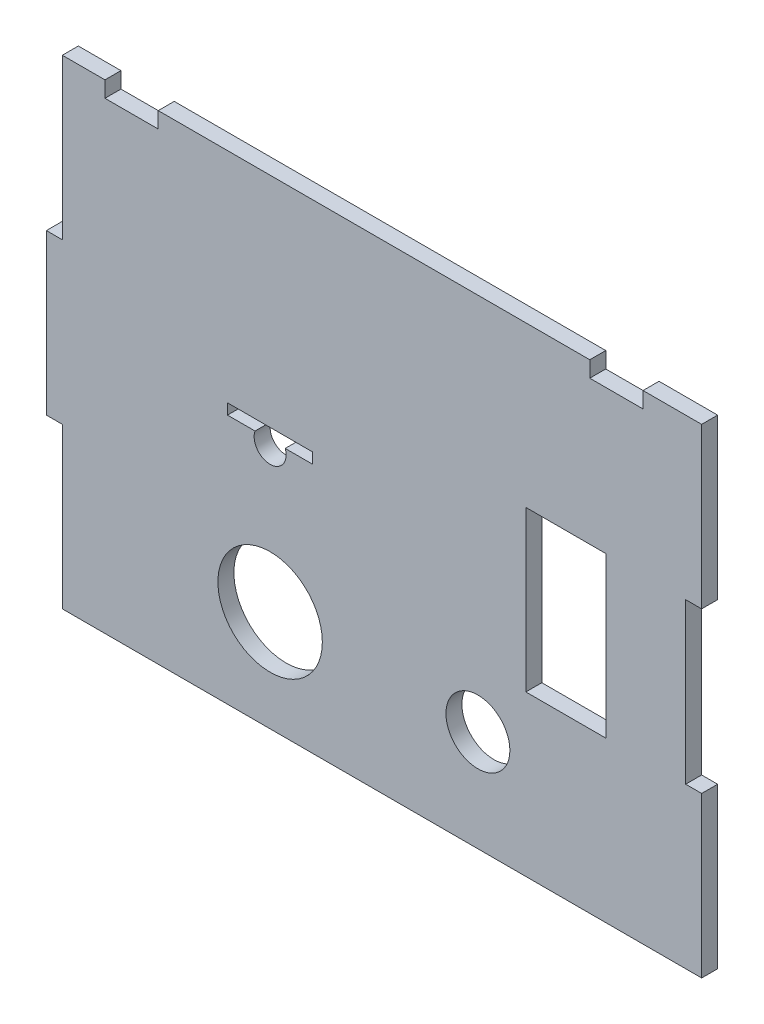
SolidWorks part; units mm, degrees
ref_plane "Front Plane" through (0, 0, 0) normal (0, 0, 1) x (1, 0, 0)
ref_plane "Top Plane" through (0, 0, 0) normal (0, 1, 0) x (1, 0, 0)
ref_plane "Right Plane" through (0, 0, 0) normal (1, 0, 0) x (0, 0, -1)
sketch "Model" plane through (0, 0, 0) normal (0, 0, 1) x (1, 0, 0)
  line L5 (-252.1919, 3) -> (-157.1919, 3) construction
  line L6 (-160.1919, -27) -> (-160.1919, -57)
  line L7 (-160.1919, -57) -> (-157.1919, -57)
  line L9 (-157.1919, -27) -> (-160.1919, -27)
  line L13 (-157.1919, -87) -> (-277.1919, -87)
  line L14 (-252.1919, 3) -> (-277.1919, 3) construction
  line L15 (-175.1919, -57) -> (-190.1919, -57)
  line L16 (-175.1919, -57) -> (-175.1919, -27)
  line L17 (-175.1919, -27) -> (-190.1919, -27)
  line L18 (-190.1919, -57) -> (-190.1919, -27)
  line L19 (-175.1919, -57) -> (-190.1919, -27) construction
  line L20 (-175.1919, -27) -> (-190.1919, -57) construction
  line L22 (-235.3635, -40) -> (-230.1919, -40)
  line L27 (-246.1919, -40) -> (-241.0204, -40)
  line L28 (-246.1919, -40) -> (-246.1919, -38)
  line L33 (-246.1919, -38) -> (-230.1919, -38)
  line L34 (-230.1919, -40) -> (-230.1919, -38)
  line L39 (-246.1919, -40) -> (-230.1919, -38) construction
  line L40 (-246.1919, -38) -> (-230.1919, -40) construction
  line L45 (-238.1919, -41) -> (-238.1919, -38) construction
  line L46 (-238.1919, -68) -> (-238.1919, -41) construction
  line L51 (-277.1919, 3) -> (-269.1919, 3)
  line L52 (-269.1919, 3) -> (-269.1919, 0)
  line L57 (-269.1919, 0) -> (-259.1919, 0)
  line L58 (-259.1919, 0) -> (-259.1919, 3)
  line L59 (-259.1919, 3) -> (-178.1919, 3)
  line L60 (-157.1919, -57) -> (-157.1919, -87)
  line L65 (-178.1919, 3) -> (-178.1919, 0)
  line L66 (-178.1919, 0) -> (-168.1919, 0)
  line L67 (-157.1919, -27) -> (-157.1919, 3)
  line L68 (-168.1919, 0) -> (-168.1919, 3)
  line L69 (-168.1919, 3) -> (-157.1919, 3)
  line L134 (-277.1919, -87) -> (-277.1919, -57)
  line L135 (-277.1919, -57) -> (-280.1919, -57)
  line L136 (-280.1919, -57) -> (-280.1919, -27)
  line L149 (-280.1919, -27) -> (-277.1919, -27)
  line L150 (-277.1919, -27) -> (-277.1919, 3)
  circle A0 centre (-238.1919, -68) radius 9.8
  circle A1 centre (-199.1919, -68) radius 6
  arc A2 (-241.0204, -40) -> (-235.3635, -40) centre (-238.1919, -41) ccw
  point P12 (-182.6919, -42)
  point P18 (-238.1919, -39)
  dimension "D6" = 3
  dimension "D10" = 30
  dimension "D11" = 3
  dimension "D3" = 30
  dimension "D4" = 120
  dimension "D5" = 30
  dimension "D7" = 19
  dimension "D9" = 2
  dimension "D12" = 30
  dimension "D13" = 3
  dimension "D14" = 30
  dimension "D15" = 3
  dimension "D16" = 10
  dimension "D17" = 10
  dimension "D18" = 11
  dimension "D19" = 8
  dimension "D20" = 3
  dimension "D21" = 15
  dimension "D22" = 30
  dimension "D23" = 15
  dimension "15.2" = 16
  dimension "81" = 81
extrude "Boss-Extrude1" add sketch "Model" along normal blind 3
